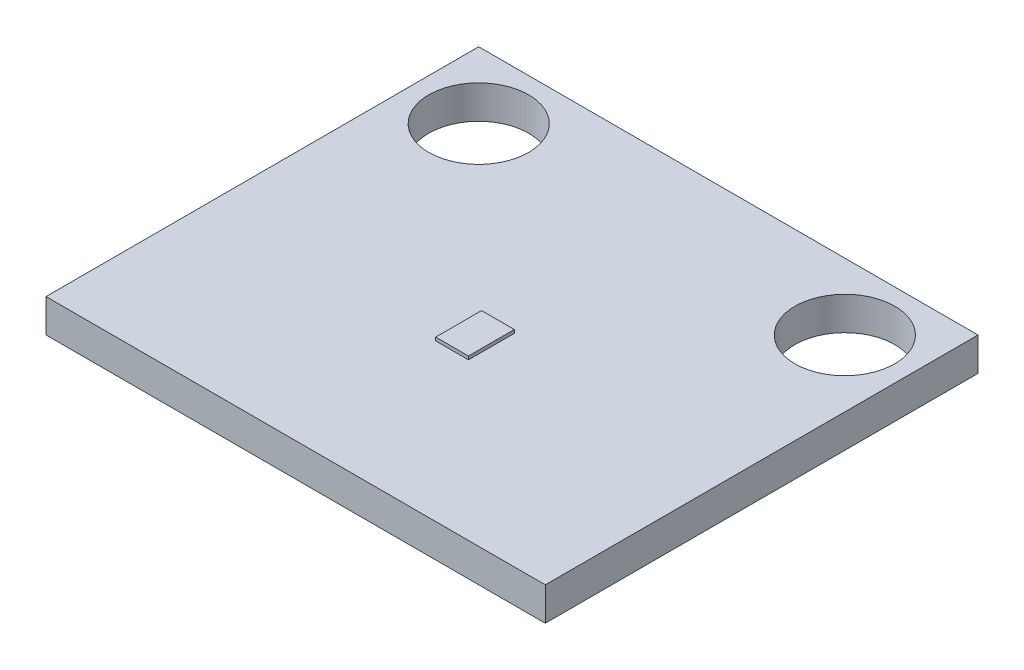
SolidWorks part; units mm, degrees
material "Silicon"
ref_plane "Front Plane" through (0, 0, 0) normal (0, 0, 1) x (1, 0, 0)
ref_plane "Top Plane" through (0, 0, 0) normal (0, 1, 0) x (1, 0, 0)
ref_plane "Right Plane" through (0, 0, 0) normal (1, 0, 0) x (0, 0, -1)
sketch "Sketch1" plane through (0, 0, 0) normal (0, 1, 0) x (1, 0, 0)
  line L1 (-7.6418, 7.2172) -> (11.4082, 7.2172)
  line L2 (-7.6418, 7.2172) -> (-7.6418, -9.2928)
  line L3 (-7.6418, -9.2928) -> (11.4082, -9.2928)
  line L4 (11.4082, 7.2172) -> (11.4082, -9.2928)
  dimension "D1" = 16.51
  dimension "D2" = 19.05
extrude "Boss-Extrude1" add sketch "Sketch1" along normal blind 1.27 contours L2 L3 L4 L1
sketch "Sketch2" plane through (0, 1.27, 0) normal (0, 1, 0) x (1, 0, 0)
  line L0 (-7.6418, 7.2172) -> (-7.6418, -9.2928) construction
  line L1 (-7.6418, -9.2928) -> (11.4082, -9.2928) construction
  circle A0 centre (-5.1018, 4.6772) radius 1.905
  circle A1 centre (8.8682, 4.6772) radius 1.905
  dimension "D4" = 3.81
  dimension "D1" = 2.54
  dimension "D2" = 13.97
  dimension "D3" = 13.97
extrude "Cut-Extrude1" cut sketch "Sketch2" against normal blind 1.27
sketch "Sketch3" plane through (0, 1.27, 0) normal (0, 1, 0) x (1, 0, 0)
  line L0 (1.8832, 7.2172) -> (1.8832, -9.2928) construction
  line L1 (1.2582, -1.5738) -> (2.5082, -1.5738)
  line L2 (1.2582, -1.5738) -> (1.2582, -3.3238)
  line L3 (1.2582, -3.3238) -> (2.5082, -3.3238)
  line L4 (2.5082, -1.5738) -> (2.5082, -3.3238)
  line L5 (-7.6418, 7.2172) -> (11.4082, 7.2172) construction
  line L6 (-7.6418, -9.2928) -> (11.4082, -9.2928) construction
  point P10 (1.8832, -1.5738)
  dimension "D1" = 1.75
  dimension "D2" = 1.25
  dimension "D3" = 5.969
extrude "Boss-Extrude2" add sketch "Sketch3" along normal blind 0.127
